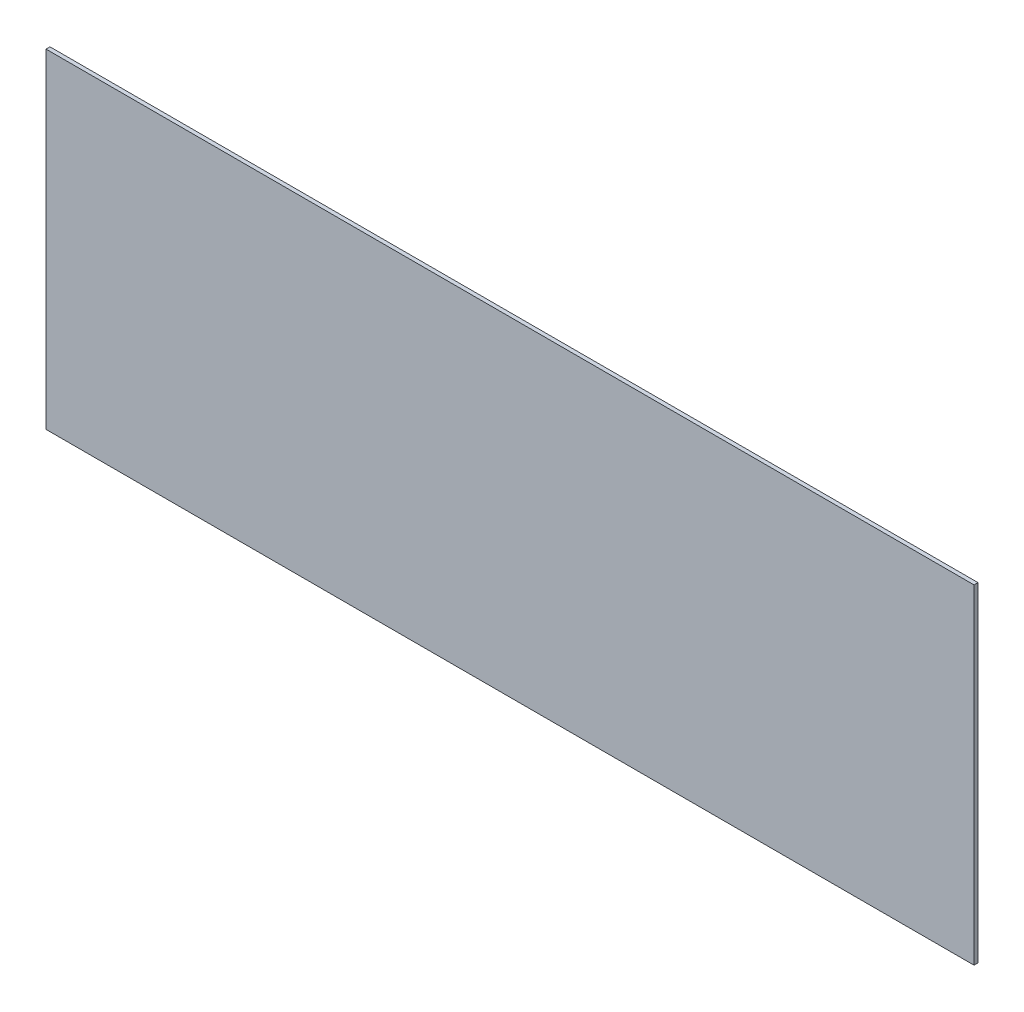
SolidWorks part; units mm, degrees
material "Mahogany"
ref_plane "Front Plane" through (0, 0, 0) normal (0, 0, 1) x (1, 0, 0)
ref_plane "Top Plane" through (0, 0, 0) normal (0, 1, 0) x (1, 0, 0)
ref_plane "Right Plane" through (0, 0, 0) normal (1, 0, 0) x (0, 0, -1)
sketch "Sketch1" plane through (0, 0, 0) normal (0, 0, 1) x (1, 0, 0)
  line L1 (-372.5, 132.2) -> (372.5, 132.2)
  line L2 (-372.5, 132.2) -> (-372.5, -132.2)
  line L3 (-372.5, -132.2) -> (372.5, -132.2)
  line L4 (372.5, 132.2) -> (372.5, -132.2)
  line L5 (-372.5, 132.2) -> (372.5, -132.2) construction
  line L6 (-372.5, -132.2) -> (372.5, 132.2) construction
  point P0 (0, 0)
  dimension "D1" = 745
  dimension "D2" = 264.4
extrude "Boss-Extrude1" add sketch "Sketch1" along normal blind 3.175
equation "\"W\"= 1700"
equation "\"L\"= 760"
equation "\"H\"= 810"
equation "\"ARM_BOLT_SPACING\"= 166"
equation "\"ARM_TO_WALL\"= 300"
equation "\"D1@Sketch1\"=\"L\"-15"
equation "\"D2@Sketch1\"=279.4-15"
